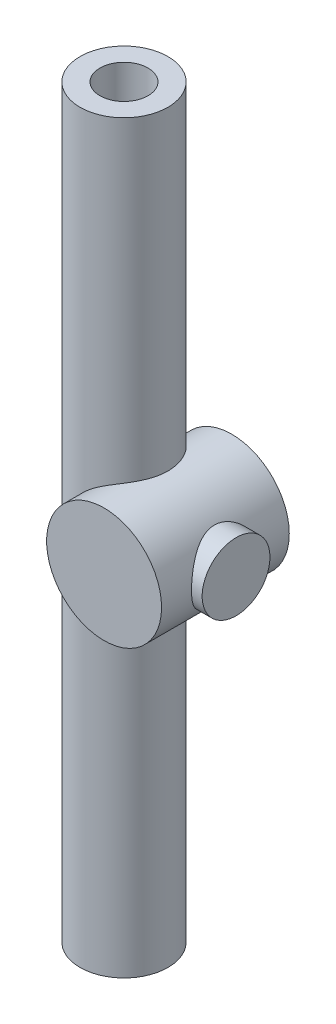
SolidWorks part; units mm, degrees
ref_plane "Front Plane" through (0, 0, 0) normal (0, 0, 1) x (1, 0, 0)
ref_plane "Top Plane" through (0, 0, 0) normal (0, 1, 0) x (1, 0, 0)
ref_plane "Right Plane" through (0, 0, 0) normal (1, 0, 0) x (0, 0, -1)
sketch "Sketch1" plane through (0, 0, 0) normal (0, 0, 1) x (1, 0, 0)
  circle A0 centre (0, 0) radius 27
  dimension "D1" = 54
extrude "Boss-Extrude1" add sketch "Sketch1" along normal blind 60
sketch "Sketch2" plane through (0, 0, 0) normal (0, 1, 0) x (1, 0, 0)
  line L0 (0, 71.8869) -> (0, -162.5592) construction
  line L1 (27, 0) -> (-27, 0) construction
  circle A0 centre (-20.65, -30) radius 20.65
  dimension "D1" = 41.3
  dimension "D2" = 30
extrude "Boss-Extrude2" add sketch "Sketch2" along normal mid plane 350
sketch "Sketch3" plane through (0, 0, 0) normal (1, 0, 0) x (0, 0, -1)
  line L0 (76.4851, 0) -> (-136.4851, 0) construction
  circle A0 centre (-30, 0) radius 15.925
  dimension "D1" = 31.85
  dimension "D2" = 30
extrude "Boss-Extrude3" add sketch "Sketch3" along normal blind 32
sketch "Sketch4" plane through (0, 175, 0) normal (0, 1, 0) x (1, 0, 0)
  circle A0 centre (-20.65, -30) radius 11.295
  dimension "D1" = 22.59
extrude "Cut-Extrude1" cut sketch "Sketch4" against normal through all
sketch "Sketch5" plane through (0, 0, 0) normal (0, 0, -1) x (-1, 0, 0)
  circle A0 centre (0, 0) radius 15.925
  dimension "D1" = 31.85
extrude "Cut-Extrude2" cut sketch "Sketch5" against normal blind 52
